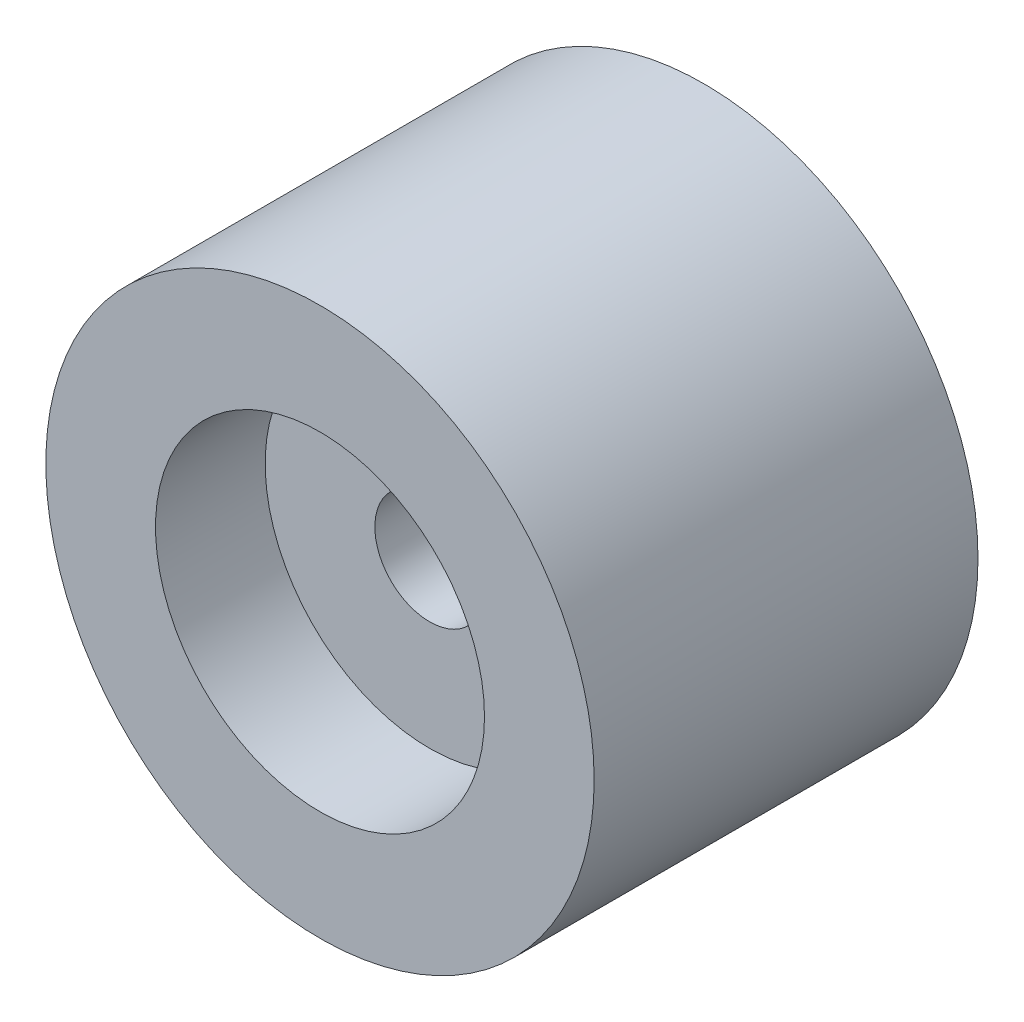
SolidWorks part; units mm, degrees
ref_plane "Front Plane" through (0, 0, 0) normal (0, 0, 1) x (1, 0, 0)
ref_plane "Top Plane" through (0, 0, 0) normal (0, 1, 0) x (1, 0, 0)
ref_plane "Right Plane" through (0, 0, 0) normal (1, 0, 0) x (0, 0, -1)
sketch "Sketch1" plane through (0, 0, 0) normal (0, 0, 1) x (1, 0, 0)
  circle A0 centre (0, 0) radius 100
extrude "Boss-Extrude1" add sketch "Sketch1" along normal blind 140
sketch "Sketch2" plane through (0, 0, 140) normal (0, 0, 1) x (1, 0, 0)
  circle A0 centre (0, 0) radius 60
extrude "Cut-Extrude1" cut sketch "Sketch2" against normal blind 40
sketch "Sketch4" plane through (0, 0, 100) normal (0, 0, 1) x (1, 0, 0)
  circle A0 centre (0, 0) radius 20
extrude "Cut-Extrude2" cut sketch "Sketch4" against normal blind 80
